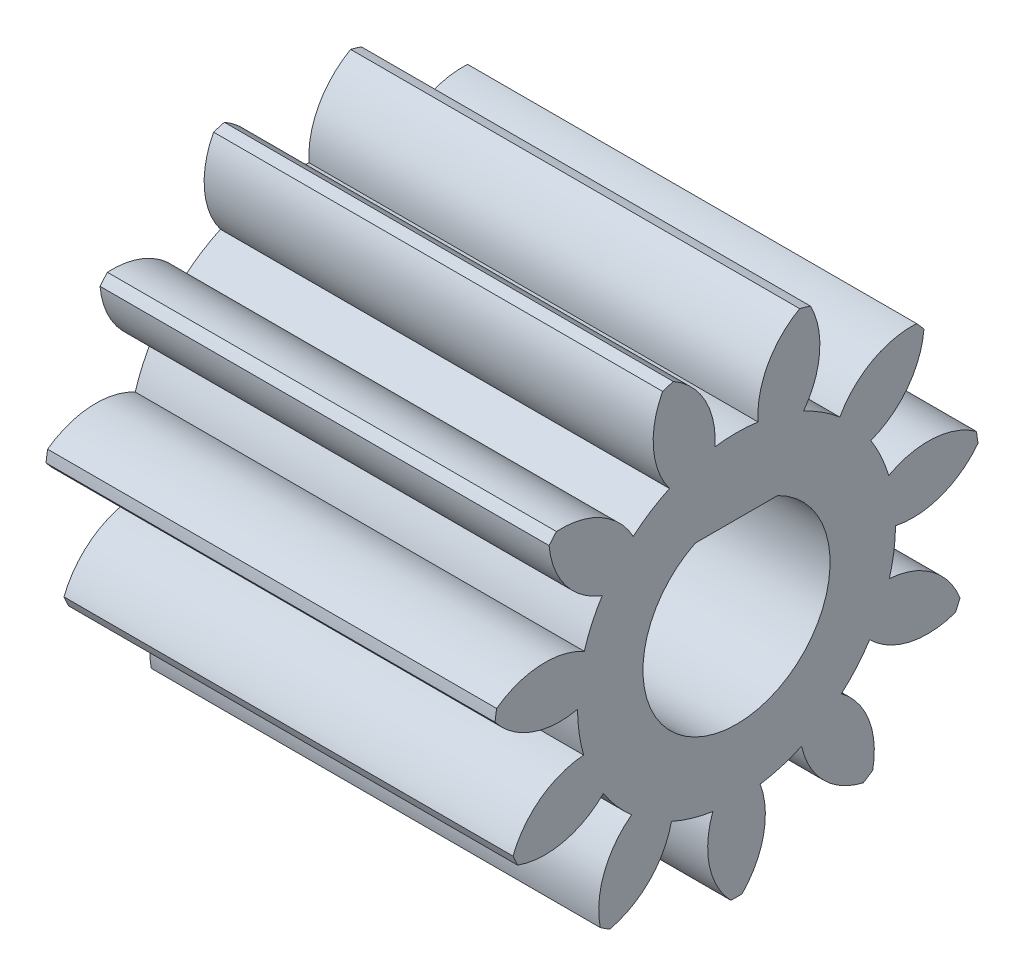
SolidWorks part; units mm, degrees
ref_plane "Plane1" through (0, 0, 0) normal (0, 0, 1) x (1, 0, 0)
ref_plane "Plane2" through (0, 0, 0) normal (0, 1, 0) x (1, 0, 0)
ref_plane "Plane3" through (0, 0, 0) normal (1, 0, 0) x (0, 0, -1)
sketch "HoldingSke" plane through (0, 0, 0) normal (0, 1, 0) x (1, 0, 0)
  line L0 (0, 0) -> (0.9816, -0.1908)
  line L1 (-15, 0) -> (100, 0) construction
  line L2 (0, 0) -> (-2.1039, 2.3779)
  line L3 (0, 0) -> (-11.863, 4.5341)
  line L4 (0, 0) -> (8.4773, 1.6478)
  line L5 (0, 0) -> (-46.8476, -17.4728)
  line L6 (0, 0) -> (-9.9476, -6.7116)
  line L7 (-2.1039, 2.3779) -> (8.6586, 51.2059)
  line L8 (-76.2, 54.61) -> (-75.3, 54.61)
  line L9 (-71.009, 38.7566) -> (-53.1078, 45.2721)
  line L10 (-76.2, 71.12) -> (104.1128, 71.12)
  line L11 (0, 0) -> (-12, 0)
  line L12 (-76.2, 101.6) -> (-76.162, 101.6)
  line L13 (24.9733, 27.94) -> (52.9518, 28.4284)
  line L14 (24.9733, 27.94) -> (24.9743, 27.94)
  line L15 (24.9733, 27.94) -> (100.4006, 29.5858)
  line L16 (-63.627, -1) -> (-12.827, -1)
  circle A0 centre (0, 0) radius 2.5
  circle A1 centre (0, 0) radius 4.249
  circle A2 centre (0, 0) radius 37.5
  circle A3 centre (0, 0) radius 2.5
  dimension "MHD" = 8.498
  dimension "Hub_dia" = 75
  dimension "Bore" = 5
  dimension "MBD" = 5
  dimension "Num_teeth" = 11
  dimension "Pitch" = 1
  dimension "Overall_len" = 50
  dimension "Show_teeth" = 11
  dimension "Thickness" = 12
  dimension "OAL" = 50.0001
  dimension "T_dim" = 0.9
  dimension "Ap" = 20
  dimension "H" = 19.05
  dimension "Pitch_radius" = 180.3128
  dimension "Width" = 12
  dimension "Backlash" = 0.038
  dimension "Addendum_fac" = 1
  dimension "Dedendum_fac" = 1.25
  dimension "Clearance_fac" = 0.25
  dimension "Dedendum_add" = 0.001
  dimension "Module" = 1
sketch "BasProSke" plane through (0, 0, 0) normal (0, 1, 0) x (1, 0, 0)
  line L0 (-10, 0) -> (60, 0) construction
  line L1 (0, 0) -> (0, 6.5)
  line L2 (0, 0) -> (12, 0)
  line L3 (12, 0) -> (12, 6.5)
  line L4 (12, 6.5) -> (0, 6.5)
  dimension "Thickness" = 12
  dimension "Diameter" = 13
revolve "Base-Revolve" add sketch "BasProSke" angle 360 about L0
sketch "TooCutSke" plane through (0, 0, 0) normal (1, 0, 0) x (0, 0, -1)
  line L1 (0, 0) -> (0, 107) construction
  line L2 (0, 0) -> (-0.8491, 5.4341) construction
  line L3 (0, 0) -> (-3.0727, 10.4645) construction
  line L4 (-0.8491, 5.4341) -> (-1.5363, 5.2323) construction
  arc A0 (0.576, 4.2098) -> (-0.576, 4.2098) centre (0, 0) ccw
  arc A1 (1.7187, 6.295) -> (-1.7187, 6.295) centre (0, 0) ccw
  circle A2 centre (0, 0) radius 5.5 construction
  circle A3 centre (0, 0) radius 5.1683 construction
  arc A4 (-0.576, 4.2098) -> (-1.7187, 6.295) centre (-2.7707, 4.3629) ccw
  arc A5 (1.7187, 6.295) -> (0.576, 4.2098) centre (2.7707, 4.3629) ccw
  dimension "Root_dia" = 8.498
  dimension "Overcut_dia" = 13.0508
  dimension "Pitch_dia" = 11
  dimension "Base_dia" = 10.3366
  dimension "Flank_rad" = 2.2
  dimension "Half_ang" = 16.364
  dimension "Half_CT" = 0.7162
extrude "ToothCut" cut sketch "TooCutSke" along normal through all
fillet "Breaks" [suppressed] radius 0.02
fillet "RootFillets" [suppressed] radius 0.251
pattern_circular "TeethCuts" count 11 every 32.727 about axis through (-10, 0, 0) along (1, 0, 0) of "ToothCut", "RootFillets", "Breaks"
sketch "HubNeaOneSke" plane through (0, 0, 0) normal (-1, 0, 0) x (0, 0, 1)
  circle A0 centre (0, 0) radius 4.249
  dimension "Diameter" = 8.498
extrude "HubNearOne" [suppressed] add sketch "HubNeaOneSke" along normal blind 38.0001
sketch "HubNeaBotSke" plane through (0, 0, 0) normal (-1, 0, 0) x (0, 0, 1)
  circle A0 centre (0, 0) radius 4.249
  dimension "Diameter" = 8.498
extrude "HubNearBoth" [suppressed] add sketch "HubNeaBotSke" along normal blind 19
ref_plane "FarPln" through (12, 0, 0) normal (1, 0, 0) x (0, 0, -1)
sketch "HubFarSke" plane through (12, 0, 0) normal (1, 0, 0) x (0, 0, -1)
  circle A0 centre (0, 0) radius 4.249
  dimension "Diameter" = 8.498
extrude "HubFar" [suppressed] add sketch "HubFarSke" along normal blind 19
sketch "BorSke" plane through (0, 0, 0) normal (1, 0, 0) x (0, 0, -1)
  circle A0 centre (0, 0) radius 2.5
  dimension "Diameter" = 5
extrude "Bore" cut sketch "BorSke" along normal mid plane 100.0001
sketch "KeySke" plane through (0, 0, 0) normal (1, 0, 0) x (0, 0, -1)
  line L0 (-1, 0) -> (-1, 3.4)
  line L1 (-1, 3.4) -> (1, 3.4)
  line L2 (1, 3.4) -> (1, 0)
  line L3 (0, 0) -> (0, 34) construction
  line L4 (-1, 0) -> (1, 0)
  dimension "Offset" = 3.4
  dimension "Width" = 2
extrude "Keyway" [suppressed] cut sketch "KeySke" along normal mid plane 100.0001
pattern_circular "Keyway2" [suppressed] count 2 every 90 about axis through (-10, 0, 0) along (1, 0, 0)
sketch "Sketch1" plane through (12, 0, 0) normal (1, 0, 0) x (0, 0, -1)
  line L0 (-1.1, 2.245) -> (1.1, 2.245)
  circle A0 centre (0, 0) radius 2.5 construction
  circle A2 centre (0, 0) radius 2.5
  arc A3 (1.1, 2.245) -> (-1.1, 2.245) centre (0, 0) ccw
  dimension "D1" = 0
extrude "Boss-Extrude1" add sketch "Sketch1" against normal blind 12
equation "' \"Module@HoldingSke\" = 6.35"
equation "' \"Num_teeth@HoldingSke\" = 12"
equation "' \"Ap@HoldingSke\" =  20"
equation "' \"Ap@HoldingSke\" = 20"
equation "' \"Width@HoldingSke\" = 0.5 * 25.4"
equation "' \"Hub_dia@HoldingSke\"= 1 * 25.4"
equation "' \"Hub_dia@HoldingSke\" = 1 * 25.4"
equation "' \"Overall_len@HoldingSke\" = 1.0 * 25.4"
equation "' \"Bore@HoldingSke\" = 0.75 * 25.4"
equation "' \"T_dim@HoldingSke\" = 0.1 * 25.4"
equation "' \"Width@KeySke\" = 0.25 * 25.4"
equation "' \"Show_teeth@HoldingSke\" = 13"
equation "' \"Backlash@HoldingSke\" = 0.009 * 25.4"
equation "' \"Addendum_fac@HoldingSke\" = 1.0"
equation "' \"Dedendum_fac@HoldingSke\" = 1.25"
equation "' \"Dedendum_add@HoldingSke\" = 0.00005 * 25.4"
equation "' \"Clearance_fac@HoldingSke\" = 0.25"
equation "\"Pitch@HoldingSke\" = 1 / \"Module@HoldingSke\""
equation "\"Overcut_dia@TooCutSke\" = (\"Num_teeth@HoldingSke\" + 2 * \"Addendum_fac@HoldingSke\") / \"Pitch@HoldingSke\" + 0.002 * 25.4"
equation "\"Pitch_dia@TooCutSke\" = \"Num_teeth@HoldingSke\" / \"Pitch@HoldingSke\""
equation "\"Base_dia@TooCutSke\" = \"Num_teeth@HoldingSke\" / \"Pitch@HoldingSke\" * cos((\"Ap@HoldingSke\"  * 3.14159265 / 180))"
equation "\"Root_dia@TooCutSke\" = (\"Num_teeth@HoldingSke\" + 2) / \"Pitch@HoldingSke\" - 2 * (\"Addendum_fac@HoldingSke\" + \"Dedendum_fac@HoldingSke\") / \"Pitch@HoldingSke\" - \"Dedendum_add@HoldingSke\" * 2"
equation "\"Half_ang@TooCutSke\" = 180 / \"Num_teeth@HoldingSke\""
equation "\"Half_CT@TooCutSke\" = \"Num_teeth@HoldingSke\" / \"Pitch@HoldingSke\" * sin((3.14159265 / 2 / \"Num_teeth@HoldingSke\")) / 2 - 7 * \"Backlash@HoldingSke\" / 4"
equation "\"Flank_rad@TooCutSke\" = \"Num_teeth@HoldingSke\" / \"Pitch@HoldingSke\" / 5"
equation "\"Radius@RootFillets\" = \"Clearance_fac@HoldingSke\" / \"Pitch@HoldingSke\" + \"Dedendum_add@HoldingSke\""
equation "\"Break_rad@Breaks\" = 0.02 / \"Pitch@HoldingSke\""
equation "\"Thickness@HoldingSke\" = \"Width@HoldingSke\""
equation "\"OAL@HoldingSke\" = \"Thickness@HoldingSke\""
equation "\"MHD@HoldingSke\" = (\"Num_teeth@HoldingSke\" + 2) / \"Pitch@HoldingSke\" - 2 * (\"Addendum_fac@HoldingSke\" + \"Dedendum_fac@HoldingSke\")  / \"Pitch@HoldingSke\" - \"Dedendum_add@HoldingSke\" * 2"
equation "\"MBD@HoldingSke\" = (\"Num_teeth@HoldingSke\" + 2) / \"Pitch@HoldingSke\" - 2 * (\"Addendum_fac@HoldingSke\" + \"Dedendum_fac@HoldingSke\")  / \"Pitch@HoldingSke\" - \"Dedendum_add@HoldingSke\" * 2 - 0.002 * 25.4"
equation "\"MHD@HoldingSke\" = ((sgn( \"MHD@HoldingSke\" - \"Hub_dia@HoldingSke\" )-1)*( \"MHD@HoldingSke\" - \"Hub_dia@HoldingSke\" ))/-2+ \"Hub_dia@HoldingSke\""
equation "\"MBD@HoldingSke\" = ((sgn( \"MBD@HoldingSke\" - \"Bore@HoldingSke\" )-1)*( \"MBD@HoldingSke\" - \"Bore@HoldingSke\" ))/-2+ \"Bore@HoldingSke\""
equation "\"OAL@HoldingSke\" = ((sgn( \"OAL@HoldingSke\" - \"Overall_len@HoldingSke\" )+1)*( \"OAL@HoldingSke\" - \"Overall_len@HoldingSke\" ))/2 + \"Overall_len@HoldingSke\" + 0.000002 * 25.4"
equation "\"Num_teeth@TeethCuts\" = int( \"Show_teeth@HoldingSke\" ) + 1"
equation "\"Num_teeth@TeethCuts\" = ((sgn( \"Num_teeth@TeethCuts\" - \"Num_teeth@HoldingSke\" )-1)*( \"Num_teeth@TeethCuts\" - \"Num_teeth@HoldingSke\" ))/-2+ \"Num_teeth@HoldingSke\""
equation "\"Num_teeth@TeethCuts\" = ((sgn( \"Num_teeth@TeethCuts\" - 2.0)+1)*( \"Num_teeth@TeethCuts\" - 2.0))/2 +2.0"
equation "\"Angle@TeethCuts\" = 360.0 / \"Num_teeth@HoldingSke\""
equation "\"Diameter@BasProSke\" = (\"Num_teeth@HoldingSke\" + 2 * \"Addendum_fac@HoldingSke\") / \"Pitch@HoldingSke\""
equation "\"Thickness@BasProSke\"  = \"Thickness@HoldingSke\""
equation "' \"Fillet_rad@BasProSke\" =  \"Thickness@HoldingSke\" * 0.05"
equation "' \"Fillet_rad@BasProSke\" = \"Thickness@HoldingSke\" * 0.05"
equation "\"MHD@HoldingSke\" = ((sgn( \"MHD@HoldingSke\" - \"Root_dia@TooCutSke\" )-1)*( \"MHD@HoldingSke\" - \"Root_dia@TooCutSke\" ))/-2+ \"Root_dia@TooCutSke\""
equation "\"Diameter@HubNeaOneSke\" = \"MHD@HoldingSke\""
equation "\"Length@HubNearOne\" = \"OAL@HoldingSke\" - \"Thickness@BasProSke\""
equation "\"Diameter@HubNeaBotSke\" = \"MHD@HoldingSke\""
equation "\"Length@HubNearBoth\" = ( \"OAL@HoldingSke\" - \"Thickness@BasProSke\" ) / 2.0"
equation "\"Thickness@FarPln\" = \"Thickness@BasProSke\""
equation "\"Diameter@HubFarSke\" = \"MHD@HoldingSke\""
equation "\"Length@HubFar\" = ( \"OAL@HoldingSke\" - \"Thickness@BasProSke\" ) / 2.0"
equation "\"Diameter@BorSke\" = \"MBD@HoldingSke\""
equation "\"D1@Bore\" = \"OAL@HoldingSke\" * 2.0"
equation "\"D1@Keyway\" = \"OAL@HoldingSke\" * 2.0"
equation "\"Offset@KeySke\" = \"T_dim@HoldingSke\" + \"MBD@HoldingSke\" / 2.0"
